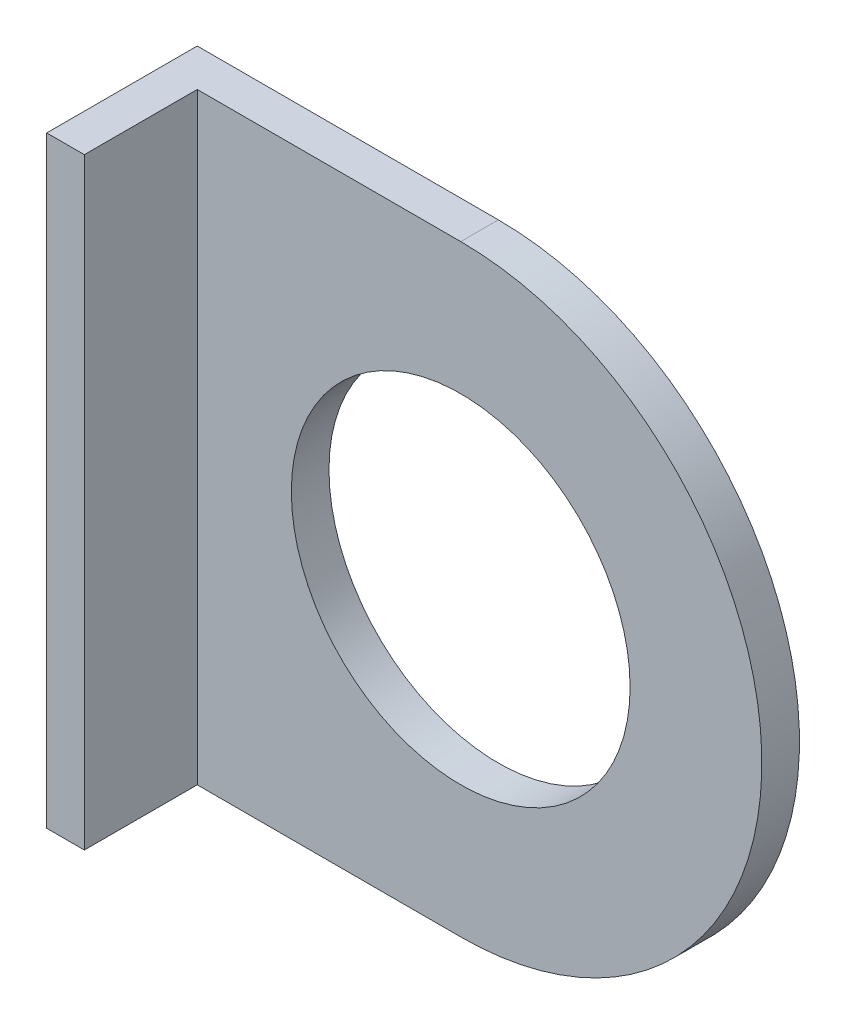
SolidWorks part; units mm, degrees
ref_plane "Front Plane" through (0, 0, 0) normal (0, 0, 1) x (1, 0, 0)
ref_plane "Top Plane" through (0, 0, 0) normal (0, 1, 0) x (1, 0, 0)
ref_plane "Right Plane" through (0, 0, 0) normal (1, 0, 0) x (0, 0, -1)
sketch "Sketch1" plane through (0, 0, 309.2672) normal (0, 0, 1) x (1, 0, 0)
  line L0 (51.9768, -201.4847) -> (51.9768, -150.6847)
  line L1 (51.9768, -150.6847) -> (77.3768, -150.6847)
  line L2 (77.3768, -201.4847) -> (51.9768, -201.4847)
  arc A0 (77.3768, -150.6847) -> (77.3768, -201.4847) centre (77.3768, -176.0847) cw
  circle A10 centre (77.3768, -176.0847) radius 14.2875
  arc A11 (40.8458, -174.0872) -> (12.3078, -174.0872) centre (26.5768, -174.8147) ccw construction
  arc A12 (40.8458, -174.0872) -> (12.3078, -174.0872) centre (26.5768, -174.8147) ccw construction
  dimension "D10" = 28.575
  dimension "D2" = 25.4
  dimension "D13" = 50.8
extrude "Boss-Extrude1" add sketch "Sketch1" along normal blind 3.175
sketch "Sketch2" plane through (0, 0, 312.4422) normal (0, 0, 1) x (1, 0, 0)
  line L0 (77.3768, -150.6847) -> (51.9768, -150.6847) construction
  line L1 (55.1518, -150.6847) -> (51.9768, -150.6847)
  line L2 (55.1518, -150.6847) -> (55.1518, -201.4847)
  line L3 (55.1518, -201.4847) -> (51.9768, -201.4847)
  line L4 (51.9768, -150.6847) -> (51.9768, -201.4847)
  dimension "D1" = 3.175
extrude "Boss-Extrude2" add sketch "Sketch2" along normal blind 9.525
